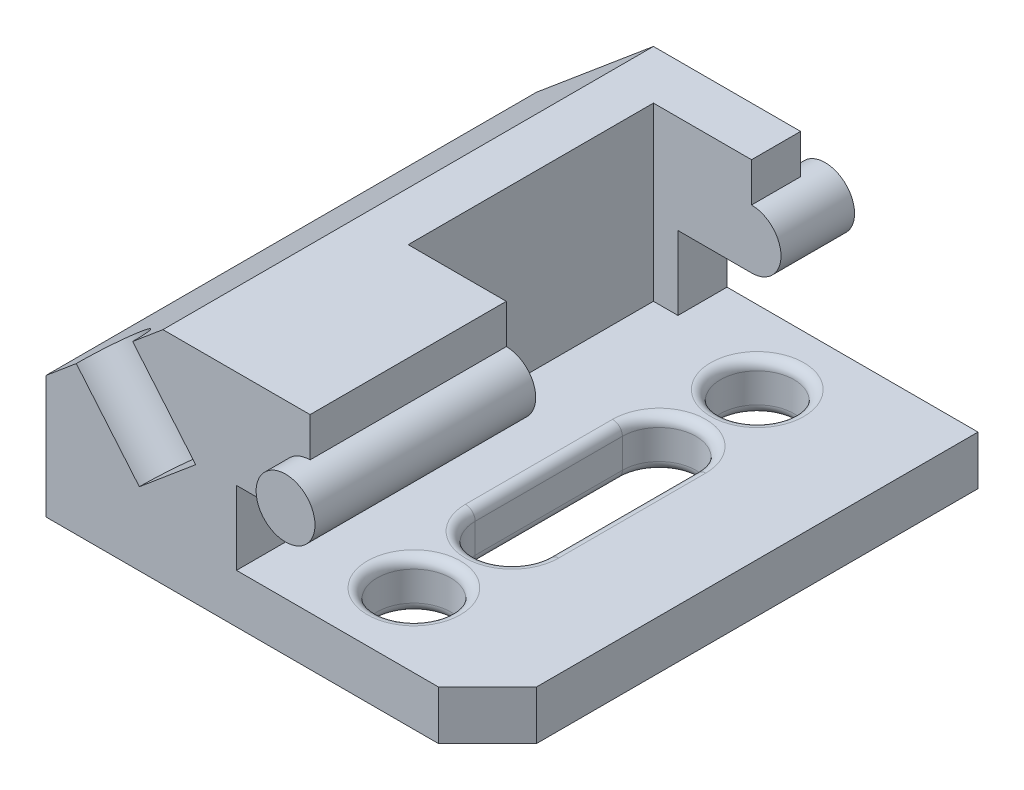
SolidWorks part; units mm, degrees
material "Stop 1060"
ref_plane "Płaszczyzna przednia" through (0, 0, 0) normal (0, 0, 1) x (1, 0, 0)
ref_plane "Płaszczyzna górna" through (0, 0, 0) normal (0, 1, 0) x (1, 0, 0)
ref_plane "Płaszczyzna prawa" through (0, 0, 0) normal (1, 0, 0) x (0, 0, -1)
sketch "Szkic2" plane through (0, 0, 0) normal (0, 0, 1) x (1, 0, 0)
  line L0 (0, 0) -> (90, 0)
  line L1 (90, 0) -> (90, 10)
  line L2 (90, 10) -> (38.8351, 10)
  line L3 (38.8351, 10) -> (38.8351, 25)
  line L4 (38.8351, 25) -> (53.8351, 25)
  line L5 (53.8351, 37) -> (53.8351, 45)
  line L6 (53.8351, 45) -> (23.8351, 45)
  line L7 (23.8351, 45) -> (0, 25)
  line L8 (0, 25) -> (0, 0)
  arc A0 (53.8351, 25) -> (53.8351, 37) centre (53.8351, 31) ccw
  point P9 (59.8351, 31)
  dimension "D3" = 15
  dimension "D1" = 30
  dimension "D2" = 6
  dimension "D4" = 50
  dimension "D5" = 20
  dimension "D6" = 25
  dimension "D7" = 90
  dimension "D8" = 15
  dimension "D9" = 10
extrude "Dodanie-wyciągnięcie1" add sketch "Szkic2" along normal blind 100
chamfer "Sfazowanie1" distance 10 angle 45 1 edges at (90, 5, 100)
sketch "Szkic3" plane through (0, 0, 100) normal (0, 0, 1) x (1, 0, 0)
  circle A0 centre (53.8351, 31) radius 6
  arc A1 (53.8351, 25) -> (53.8351, 37) centre (53.8351, 31) ccw construction
  point P2 (0, 0)
extrude "Dodanie-wyciągnięcie2" add sketch "Szkic3" along normal blind 5 and the other way blind 105 contours A0
sketch "Szkic4" plane through (0, 45, 0) normal (0, 1, 0) x (1, 0, 0)
  line L0 (23.8351, -100) -> (23.8351, 0) construction
  line L1 (33.8351, -10) -> (59.8351, -10)
  line L2 (33.8351, -10) -> (33.8351, -60)
  line L3 (33.8351, -60) -> (59.8351, -60)
  line L4 (59.8351, -10) -> (59.8351, -60)
  line L5 (59.8351, -105) -> (59.8351, 5) construction
  line L6 (53.8351, 0) -> (23.8351, 0) construction
  dimension "D1" = 10
  dimension "D2" = 50
  dimension "D3" = 10
extrude "Wytnij-wyciągnięcie1" cut sketch "Szkic4" against normal up to surface (35 mm away) up to face at (67.534, 10, 58)
sketch "Szkic5" plane through (0, 10, 0) normal (0, 1, 0) x (1, 0, 0)
  line L1 (80, -100) -> (38.8351, -100) construction
  line L2 (90, -90) -> (90, 0) construction
  line L3 (52.5, -35) -> (52.5, -65)
  line L4 (67.5, -35) -> (67.5, -65)
  circle A0 centre (60, -15) radius 7.5
  arc A1 (67.5, -35) -> (52.5, -35) centre (60, -35) ccw
  arc A2 (52.5, -65) -> (67.5, -65) centre (60, -65) ccw
  circle A3 centre (60, -85) radius 7.5
  dimension "D1" = 15
  dimension "D2" = 15
  dimension "D3" = 15
  dimension "D4" = 15
  dimension "D5" = 15
  dimension "D6" = 20
  dimension "D7" = 20
  dimension "D8" = 15
  dimension "D9" = 30
  dimension "D10" = 30
extrude "Wytnij-wyciągnięcie3" cut sketch "Szkic5" against normal through all
fillet "Zaokrąglenie2" radius 2 12 edges at (60, 0, 27.5) (60, 10, 27.5) (67.5, 0, 50) (67.5, 10, 50) (60, 0, 72.5) (60, 10, 72.5) (52.5, 0, 50) (52.5, 10, 50) (52.5, 10, 85) (52.5, 0, 85) (52.5, 10, 15) (52.5, 0, 15)
sketch "Szkic6" plane through (-12.3101, 14.6706, 0) normal (-0.6428, 0.766, 0) x (0.766, 0.6428, 0)
  line L0 (47.1842, -100) -> (16.0697, -100) construction
  circle A0 centre (31.6269, -100) radius 7.5
  point P2 (0, 0)
  point P6 (31.6269, -100)
  dimension "D1" = 15
extrude "Wytnij-wyciągnięcie5" cut sketch "Szkic6" against normal blind 20
